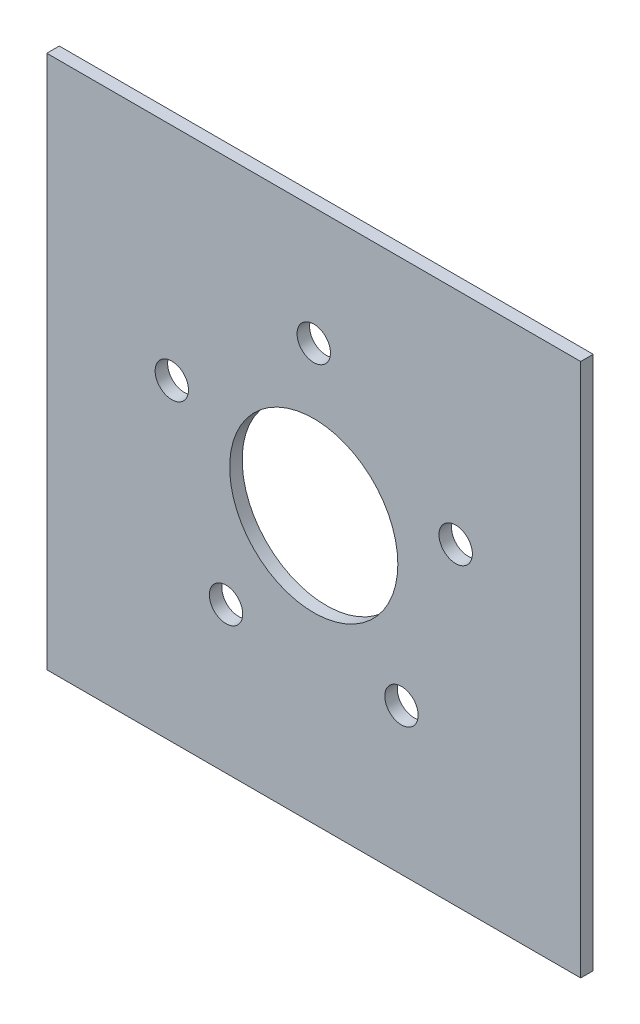
SolidWorks part; units mm, degrees
material "ASTM A36 Steel"
ref_plane "Front Plane" through (0, 0, 0) normal (0, 0, 1) x (1, 0, 0)
ref_plane "Top Plane" through (0, 0, 0) normal (0, 1, 0) x (1, 0, 0)
ref_plane "Right Plane" through (0, 0, 0) normal (1, 0, 0) x (0, 0, -1)
sketch "Sketch2" plane through (0, 0, 0) normal (0, 0, 1) x (1, 0, 0)
  circle A2 centre (0, 0) radius 80.645
  circle A9 centre (-33.3856, -45.9513) radius 6.35
  circle A10 centre (33.3856, -45.9513) radius 6.35
  circle A11 centre (54.019, 17.5518) radius 6.35
  circle A12 centre (0, 56.7989) radius 6.35
  circle A13 centre (-54.019, 17.5518) radius 6.35
sketch "Sketch4" plane through (0, 0, 0) normal (0, 0, 1) x (1, 0, 0)
  line L1 (101.6, 101.6) -> (-101.6, 101.6)
  line L2 (101.6, 101.6) -> (101.6, -101.6)
  line L3 (101.6, -101.6) -> (-101.6, -101.6)
  line L4 (-101.6, 101.6) -> (-101.6, -101.6)
  line L5 (101.6, 101.6) -> (-101.6, -101.6) construction
  line L6 (101.6, -101.6) -> (-101.6, 101.6) construction
  circle A1 centre (-54.019, 17.5518) radius 6.35 construction
  circle A2 centre (0, 56.7989) radius 6.35 construction
  circle A3 centre (-33.3856, -45.9513) radius 6.35 construction
  circle A4 centre (33.3856, -45.9513) radius 6.35 construction
  circle A5 centre (54.019, 17.5518) radius 6.35 construction
  circle A6 centre (-54.019, 17.5518) radius 6.35
  circle A7 centre (0, 56.7989) radius 6.35
  circle A8 centre (-33.3856, -45.9513) radius 6.35
  circle A9 centre (33.3856, -45.9513) radius 6.35
  circle A10 centre (54.019, 17.5518) radius 6.35
  circle A11 centre (0, 0) radius 32.004
  point P0 (0, 0)
  dimension "D3" = 64.008
  dimension "D1" = 203.2
  dimension "D2" = 203.2
extrude "Boss-Extrude1" add sketch "Sketch4" along normal blind 4.7625
